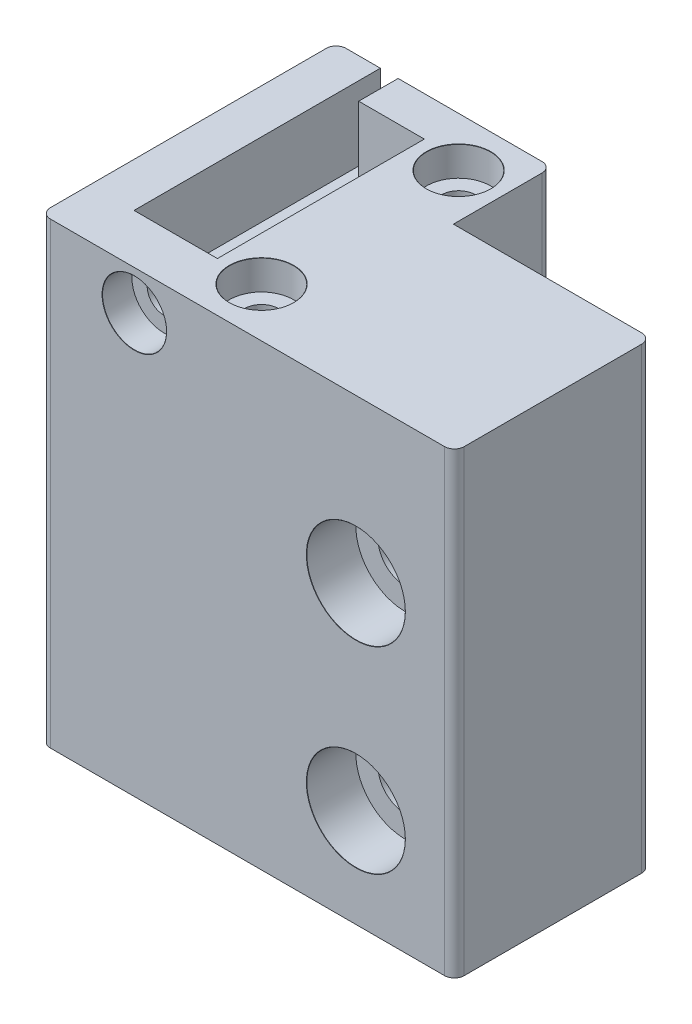
SolidWorks part; units mm, degrees
ref_plane "Front Plane" through (0, 0, 0) normal (0, 0, 1) x (1, 0, 0)
ref_plane "Top Plane" through (0, 0, 0) normal (0, 1, 0) x (1, 0, 0)
ref_plane "Right Plane" through (0, 0, 0) normal (1, 0, 0) x (0, 0, -1)
sketch "Sketch1" plane through (0, 0, 0) normal (0, 1, 0) x (1, 0, 0)
  line L1 (21, 10) -> (-21, 10)
  line L2 (21, 10) -> (21, -10)
  line L3 (21, -10) -> (-21, -10)
  line L4 (-21, 10) -> (-21, -10)
  line L5 (21, 10) -> (-21, -10) construction
  line L6 (21, -10) -> (-21, 10) construction
  point P0 (0, 0)
  dimension "D1" = 20
  dimension "D2" = 42
extrude "Boss-Extrude1" add sketch "Sketch1" along normal blind 40
sketch "Sketch2" plane through (0, 0, 10) normal (0, 0, 1) x (1, 0, 0)
  line L0 (21, 20) -> (-21, 20) construction
  line L3 (21, 40) -> (21, 0) construction
  line L4 (-21, 40) -> (-21, 0) construction
  line L5 (11, 30) -> (11, 10)
  point P9 (11, 20)
  dimension "D1" = 20
  dimension "D2" = 10
hole_wizard "CBORE for M5 SHCS1" positions "Sketch3" profile "Sketch4" counterbore size "M5" standard "ANSI Metric" end condition through all
sketch "Sketch3" plane through (0, 0, 10) normal (0, 0, 1) x (1, 0, 0)
  point P0 (11, 30)
  point P3 (11, 10)
sketch "Sketch4" plane through (11, 30, 10) normal (1, 0, 0) x (0, -1, 0)
  line L0 (0, 0) -> (0, 20)
  line L1 (0, 20) -> (2.75, 20)
  line L3 (2.75, 20) -> (2.75, 5)
  line L4 (5, 5) -> (2.75, 5)
  line L5 (5, 5) -> (5, 0.021)
  line L6 (5, 0.021) -> (5.025, 0)
  line L7 (5.025, 0) -> (0, 0)
  line L8 (-5, 0.021) -> (-5.025, 0) construction
  line L11 (0, -6.35) -> (0, 107.95) construction
  dimension "Thru Hole Dia." = 5.5
  dimension "Thru Hole Depth" = 20
  dimension "C'Bore Dia." = 10
  dimension "C'Bore Depth" = 5
  dimension "Near C'Sink Dia." = 10.05
  dimension "Near C'Sink Angle" = 100
sketch "Sketch5" plane through (0, 40, 0) normal (0, 1, 0) x (1, 0, 0)
  line L4 (-21, 10) -> (-21, -10)
  line L5 (-21, -10) -> (21, -10)
  line L6 (21, -10) -> (21, 10)
  line L7 (21, 10) -> (-21, 10)
  line L8 (-21, 10) -> (-21, -10)
  line L9 (-21, -10) -> (21, -10)
  line L10 (21, -10) -> (21, 10)
  line L11 (21, 10) -> (-21, 10)
  dimension "D1" = 0
extrude "Boss-Extrude2" add sketch "Sketch5" along normal blind 6.5
sketch "Sketch12" plane through (0, 46.5, 0) normal (0, 1, 0) x (1, 0, 0)
  line L0 (21, -10) -> (21, 10) construction
  line L1 (-21, 10) -> (0.9, 10)
  line L2 (-21, 10) -> (-21, 20)
  line L3 (-21, 20) -> (0.9, 20)
  line L4 (0.9, 10) -> (0.9, 20)
  dimension "D1" = 10
  dimension "D2" = 20.1
extrude "Boss-Extrude3" add sketch "Sketch12" against normal up to surface (46.5 mm away) up to face at (0, 0, 0)
sketch "Sketch6" plane through (0, 46.5, 0) normal (0, 1, 0) x (1, 0, 0)
  line L0 (-16.51, 20) -> (-16.51, -5)
  line L2 (-16.51, -5) -> (-8.05, -5)
  line L3 (-8.05, -5) -> (-8.05, 16)
  line L4 (-8.05, 16) -> (-14.71, 16)
  line L5 (-14.71, 16) -> (-14.71, 20)
  line L6 (-21, 20) -> (-21, -10) construction
  line L7 (-16.51, 20) -> (-14.71, 20)
  line L8 (21, -10) -> (-21, -10) construction
  line L9 (0.9, 20) -> (-21, 20) construction
  dimension "D1" = 4.49
  dimension "D2" = 1.8
  dimension "D3" = 5
  dimension "D4" = 8.46
  dimension "D5" = 4
extrude "Cut-Extrude1" cut sketch "Sketch6" against normal blind 7.5
fillet "Fillet1" radius 1 5 edges at (0.9, 23.25, -20) (21, 23.25, 10) (-21, 23.25, -20) (-21, 23.25, 10) (21, 23.25, -10)
sketch "Sketch7" plane through (0, 0, 10) normal (0, 0, 1) x (1, 0, 0)
  circle A0 centre (-11.48, 42.5) radius 1.65 construction
  circle A1 centre (-11.48, 42.5) radius 1.65
hole_wizard "CBORE for M3 SHCS1" positions "Sketch10" profile "Sketch11" counterbore size "M3" standard "ANSI Metric"
sketch "Sketch10" plane through (0, 0, 10) normal (0, 0, 1) x (1, 0, 0)
  point P0 (-11.48, 42.5)
sketch "Sketch11" plane through (-11.48, 42.5, 10) normal (1, 0, 0) x (0, -1, 0)
  line L0 (0, 0) -> (0, 6.0215)
  line L1 (0, 6.0215) -> (1.7, 5)
  line L2 (1.7, 5) -> (1.7, 3)
  line L3 (1.7, 3) -> (3.25, 3)
  line L5 (3.25, 3) -> (3.25, 0.021)
  line L6 (3.25, 0.021) -> (3.275, 0)
  line L7 (3.275, 0) -> (0, 0)
  line L8 (-3.25, 0.021) -> (-3.275, 0) construction
  line L10 (0, 6.0215) -> (-1.7, 5) construction
  line L11 (0, -6.35) -> (0, 107.95) construction
  dimension "Hole Dia." = 3.4
  dimension "Hole Depth" = 5
  dimension "C'Bore Dia." = 6.5
  dimension "C'Bore Depth" = 3
  dimension "Near C'Sink Dia." = 6.55
  dimension "Near C'Sink Angle" = 100
  dimension "Drill Angle" = 118
sketch "Sketch14" plane through (0, 46.5, 0) normal (0, 1, 0) x (1, 0, 0)
  line L0 (-3.575, 20) -> (-3.575, -10) construction
  line L1 (-0.1, 20) -> (-14.71, 20) construction
  line L2 (-20, -10) -> (20, -10) construction
  line L3 (0.9, 10) -> (0.9, 19) construction
  line L4 (-3.575, 15) -> (-3.575, -5) construction
  circle A0 centre (-3.575, 15) radius 2.4
  circle A1 centre (-3.575, -5) radius 2.4
  point P12 (-3.575, 5)
  dimension "D3" = 4.8
  dimension "D1" = 4.475
  dimension "D2" = 20
hole_wizard "CBORE for M3 SHCS2" positions "Sketch17" profile "Sketch16" counterbore size "M3" standard "ANSI Metric" end condition through all
sketch "Sketch17" plane through (0, 46.5, 0) normal (0, 1, 0) x (1, 0, 0)
  point P0 (-3.575, 15)
  point P3 (-3.575, -5)
sketch "Sketch16" plane through (-3.575, 46.5, -15) normal (1, 0, 0) x (0, 0, 1)
  line L0 (0, 0) -> (0, 46.5)
  line L1 (0, 46.5) -> (1.7, 46.5)
  line L3 (1.7, 46.5) -> (1.7, 3)
  line L4 (3.25, 3) -> (1.7, 3)
  line L5 (3.25, 3) -> (3.25, 0.021)
  line L6 (3.25, 0.021) -> (3.275, 0)
  line L7 (3.275, 0) -> (0, 0)
  line L8 (-3.25, 0.021) -> (-3.275, 0) construction
  line L11 (0, -6.35) -> (0, 107.95) construction
  dimension "Thru Hole Dia." = 3.4
  dimension "Thru Hole Depth" = 46.5
  dimension "C'Bore Dia." = 6.5
  dimension "C'Bore Depth" = 3
  dimension "Near C'Sink Dia." = 6.55
  dimension "Near C'Sink Angle" = 100
sketch "Sketch18" plane through (0, 0, 0) normal (0, -1, 0) x (1, 0, 0)
  line L1 (-0.475, 5) -> (-2.025, 7.6847)
  line L2 (-2.025, 7.6847) -> (-5.125, 7.6847)
  line L3 (-5.125, 7.6847) -> (-6.675, 5)
  line L4 (-6.675, 5) -> (-5.125, 2.3153)
  line L5 (-5.125, 2.3153) -> (-2.025, 2.3153)
  line L6 (-2.025, 2.3153) -> (-0.475, 5)
  line L7 (-0.475, -15) -> (-2.025, -12.3153)
  line L8 (-2.025, -12.3153) -> (-5.125, -12.3153)
  line L9 (-5.125, -12.3153) -> (-6.675, -15)
  line L10 (-6.675, -15) -> (-5.125, -17.6847)
  line L11 (-5.125, -17.6847) -> (-2.025, -17.6847)
  line L12 (-2.025, -17.6847) -> (-0.475, -15)
  line L14 (-20, 10) -> (20, 10) construction
  circle A0 centre (-3.575, 5) radius 2.6847 construction
  circle A1 centre (-3.575, -15) radius 2.6847 construction
  dimension "D1" = 3.1
extrude "Cut-Extrude2" cut sketch "Sketch18" against normal blind 8
